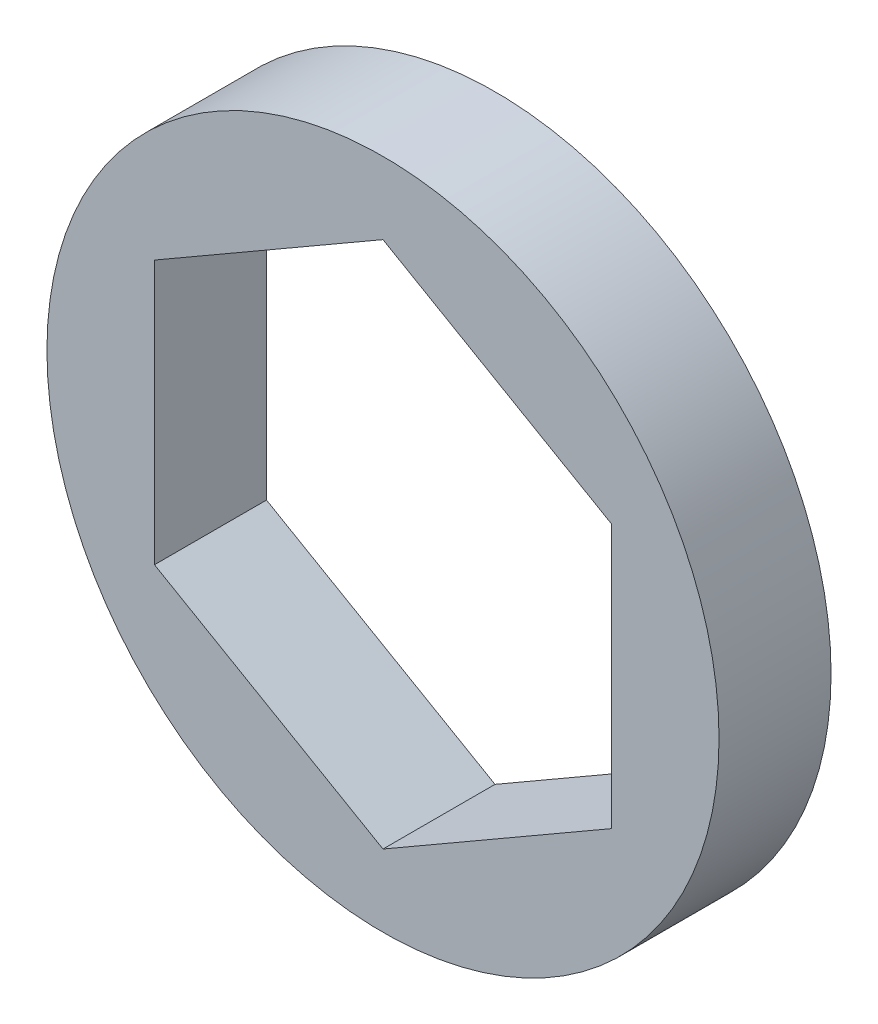
SolidWorks part; units mm, degrees
ref_plane "Front Plane" through (0, 0, 0) normal (0, 0, 1) x (1, 0, 0)
ref_plane "Top Plane" through (0, 0, 0) normal (0, 1, 0) x (1, 0, 0)
ref_plane "Right Plane" through (0, 0, 0) normal (1, 0, 0) x (0, 0, -1)
ref_plane "Plane1" through (0, 0, -1.5875) normal (0, 0, -1) x (-1, 0, 0)
sketch "Sketch1" plane through (0, 0, -1.5875) normal (0, 0, -1) x (-1, 0, 0)
  line L0 (6.477, 3.7395) -> (6.477, -3.7395)
  line L1 (6.477, -3.7395) -> (0, -7.479)
  line L2 (0, -7.479) -> (-6.477, -3.7395)
  line L3 (-6.477, -3.7395) -> (-6.477, 3.7395)
  line L4 (-6.477, 3.7395) -> (0, 7.479)
  line L5 (0, 7.479) -> (6.477, 3.7395)
  circle A0 centre (0, 0) radius 9.525
extrude "Boss-Extrude1" add sketch "Sketch1" against normal blind 3.175
